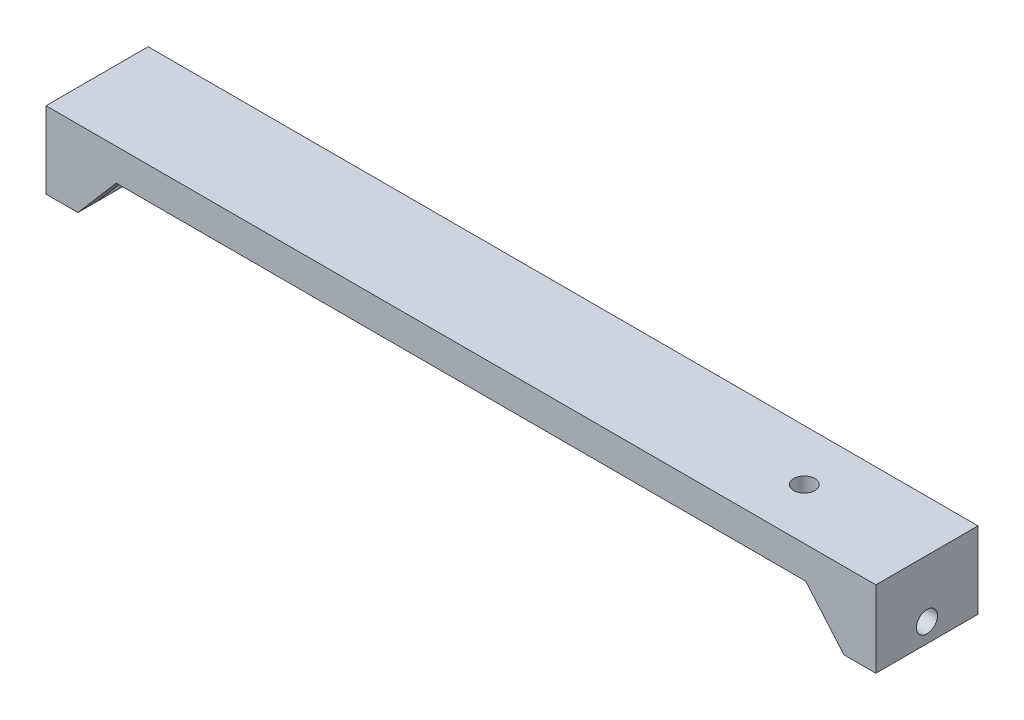
SolidWorks part; units mm, degrees
ref_plane "前视基准面" through (0, 0, 0) normal (0, 0, 1) x (1, 0, 0)
ref_plane "上视基准面" through (0, 0, 0) normal (0, 1, 0) x (1, 0, 0)
ref_plane "右视基准面" through (0, 0, 0) normal (1, 0, 0) x (0, 0, -1)
sketch "草图1" plane through (0, 0, 0) normal (0, 0, 1) x (1, 0, 0)
  line L0 (-65, 0) -> (65, 0)
  line L1 (65, 0) -> (65, -12)
  line L2 (65, -12) -> (60, -12)
  line L3 (60, -12) -> (60, -5)
  line L4 (60, -5) -> (-60, -5)
  line L5 (-60, -5) -> (-60, -12)
  line L6 (-60, -12) -> (-65, -12)
  line L7 (-65, -12) -> (-65, 0)
  line L8 (0, -7.4248) -> (0, 9.2484) construction
  dimension "D1" = 5
  dimension "D2" = 5
  dimension "D3" = 130
  dimension "D4" = 12
  dimension "D5" = 12
extrude "凸台-拉伸2" add sketch "草图1" along normal blind 16
sketch "草图3" plane through (-60, 0, 0) normal (1, 0, 0) x (0, 0, -1)
  line L1 (-16, -12) -> (0, -12) construction
  line L2 (0, 0) -> (0, -12) construction
  circle A0 centre (-8, -9) radius 1.65
  dimension "D2" = 3.3
  dimension "D1" = 3
  dimension "D3" = 8
extrude "切除-拉伸1" cut sketch "草图3" against normal through all both and the other way through all
sketch "草图4" plane through (0, 0, 0) normal (0, 0, -1) x (-1, 0, 0)
  line L0 (54, -5) -> (60, -12)
  line L1 (60, -5) -> (-60, -5) construction
  line L2 (54, -5) -> (60, -5)
  line L4 (60, -5) -> (60, -12)
  dimension "D1" = 6
extrude "凸台-拉伸3" add sketch "草图4" against normal blind 3
sketch "草图5" plane through (0, -5, 0) normal (0, -1, 0) x (1, 0, 0)
  line L0 (60, 8) -> (-60, 8) construction
  line L1 (60, 16) -> (60, 0) construction
  line L2 (-60, 16) -> (-60, 3) construction
ref_plane "基准面3" through (0, 0, 8) normal (0, 0, 1) x (1, 0, 0)
mirror "镜向1" about plane through (0, 0, 8) normal (0, 0, 1) of "凸台-拉伸3"
sketch "草图6" plane through (0, 0, 0) normal (0, 1, 0) x (1, 0, 0)
  line L0 (0, -16) -> (0, 0) construction
  line L1 (65, -16) -> (-65, -16) construction
mirror "镜向2" about plane through (0, 0, 0) normal (1, 0, 0) of "镜向1", "凸台-拉伸3"
sketch "草图7" plane through (0, 0, 0) normal (0, 1, 0) x (1, 0, 0)
  line L0 (65, -16) -> (65, 0) construction
  line L1 (65, -16) -> (-65, -16) construction
  circle A0 centre (45.79, -8) radius 1.65
  point P4 (0, 0)
  dimension "D1" = 3.3
  dimension "D2" = 19.21
  dimension "D3" = 8
extrude "切除-拉伸2" cut sketch "草图7" against normal blind 10
